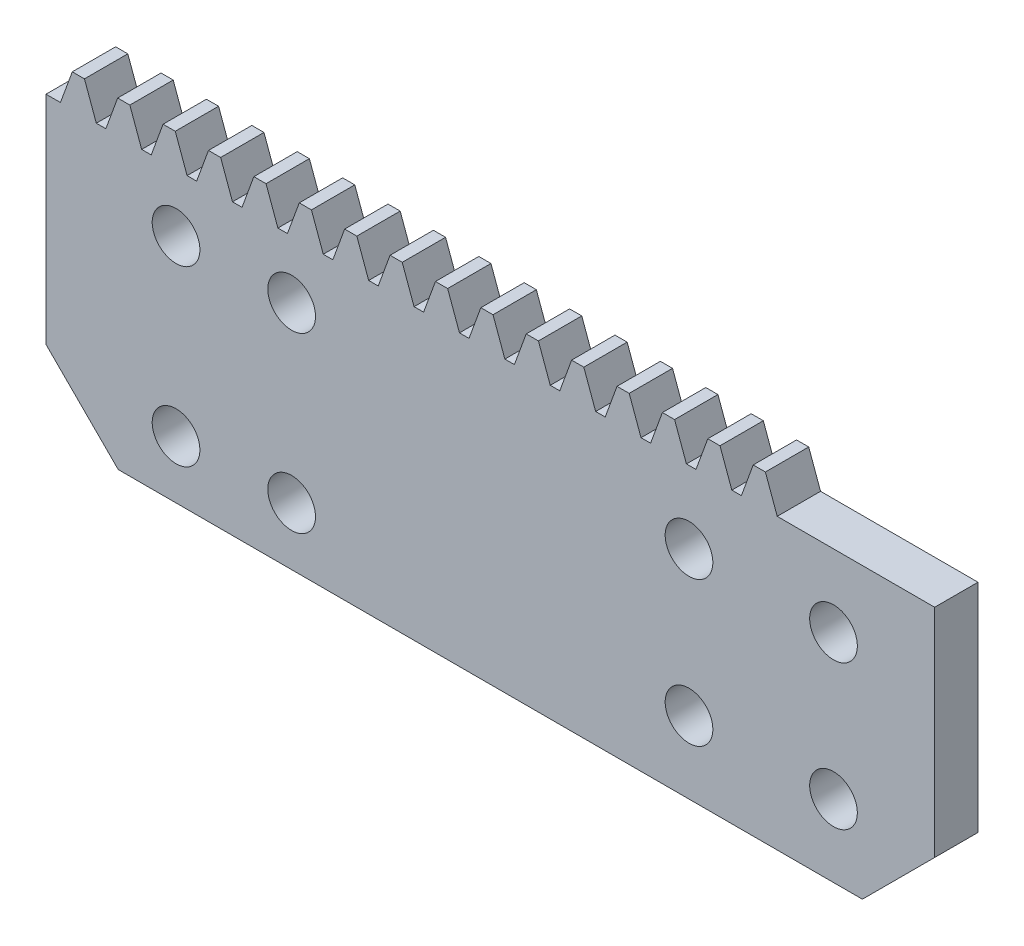
SolidWorks part; units mm, degrees
material "鑄碳鋼"
ref_plane "前基準面" through (0, 0, 0) normal (0, 0, 1) x (1, 0, 0)
ref_plane "上基準面" through (0, 0, 0) normal (0, 1, 0) x (1, 0, 0)
ref_plane "右基準面" through (0, 0, 0) normal (1, 0, 0) x (0, 0, -1)
sketch "草圖1" plane through (0, 0, 0) normal (0, 0, 1) x (1, 0, 0)
  line L1 (-30.75, -10) -> (30.75, -10)
  line L2 (-30.75, -10) -> (-30.75, 10)
  line L3 (-30.75, 10) -> (30.75, 10)
  line L4 (30.75, -10) -> (30.75, 10)
  line L5 (-30.75, -10) -> (30.75, 10) construction
  line L6 (-30.75, 10) -> (30.75, -10) construction
  point P0 (0, 0)
  dimension "D1" = 61.5
  dimension "D2" = 20
extrude "填料-伸長1" add sketch "草圖1" along normal blind 3
sketch "草圖2" plane through (0, 0, 3) normal (0, 0, 1) x (1, 0, 0)
  line L0 (-29.75, 10) -> (-28.9311, 12.25)
  line L1 (30.75, 10) -> (-30.75, 10) construction
  line L2 (-28.9311, 12.25) -> (-28.0882, 12.25)
  line L3 (-28.0882, 12.25) -> (-27.2693, 10)
  line L4 (-29.75, 10) -> (-27.2693, 10)
  line L5 (-29.295, 11.25) -> (-27.7242, 11.25) construction
  dimension "D1" = 2.25
  dimension "D2" = 40
  dimension "D3" = 1
  dimension "D4" = 1
  dimension "D5" = 1.5708
extrude "填料-伸長2" add sketch "草圖2" against normal up to surface (3 mm away) up to face at (0, 0, 0)
pattern_linear "直線複製排列1" count 16 spacing 3.1416 along (1, 0, 0) of "填料-伸長2"
sketch "草圖3" plane through (0, 0, 3) normal (0, 0, 1) x (1, 0, 0)
  line L0 (-30.75, 10) -> (-30.75, -10) construction
  line L5 (-21.75, 6) -> (-13.75, 6) construction
  line L6 (-21.75, 6) -> (-21.75, -6) construction
  line L7 (-21.75, -6) -> (-13.75, -6) construction
  line L8 (-13.75, 6) -> (-13.75, -6) construction
  circle A0 centre (-21.75, 6) radius 1.65
  circle A1 centre (-13.75, 6) radius 1.65
  circle A2 centre (-21.75, -6) radius 1.65
  circle A3 centre (-13.75, -6) radius 1.65
  point P10 (-13.75, 0)
  dimension "D2" = 3.3
  dimension "D3" = 3.3
  dimension "D4" = 3.3
  dimension "D5" = 3.3
  dimension "D1" = 8
  dimension "D6" = 9
  dimension "D7" = 12
extrude "除料-伸長1" cut sketch "草圖3" against normal up to next
sketch "草圖4" plane through (0, 0, 3) normal (0, 0, 1) x (1, 0, 0)
  line L0 (30.75, -10) -> (30.75, 10) construction
  line L1 (13.75, 5) -> (23.75, 5) construction
  line L2 (13.75, 5) -> (13.75, -5) construction
  line L3 (13.75, -5) -> (23.75, -5) construction
  line L4 (23.75, 5) -> (23.75, -5) construction
  circle A0 centre (23.75, 5) radius 1.65
  circle A1 centre (13.75, 5) radius 1.65
  circle A2 centre (23.75, -5) radius 1.65
  circle A3 centre (13.75, -5) radius 1.65
  point P11 (30.75, 0)
  point P12 (23.75, 0)
  dimension "D3" = 3.3
  dimension "D4" = 3.3
  dimension "D5" = 3.3
  dimension "D6" = 3.3
  dimension "D1" = 10
  dimension "D2" = 10
  dimension "D7" = 7
extrude "除料-伸長2" cut sketch "草圖4" against normal up to next
chamfer "導角1" distance 5 angle 45 2 edges at (30.75, -10, 1.5) (-30.75, -10, 1.5)
